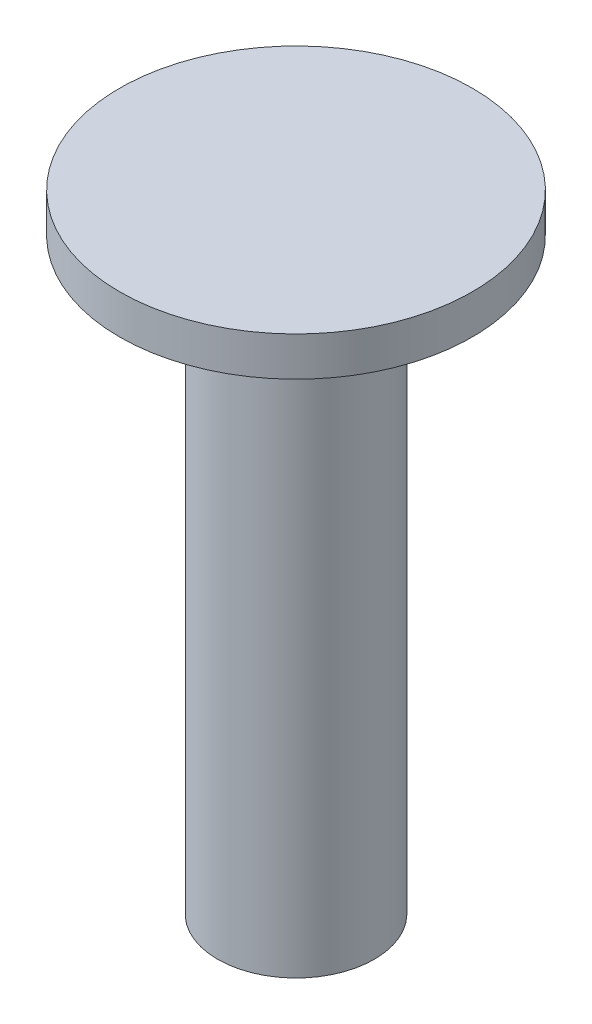
SolidWorks part; units mm, degrees
ref_plane "Front Plane" through (0, 0, 0) normal (0, 0, 1) x (1, 0, 0)
ref_plane "Top Plane" through (0, 0, 0) normal (0, 1, 0) x (1, 0, 0)
ref_plane "Right Plane" through (0, 0, 0) normal (1, 0, 0) x (0, 0, -1)
sketch "Sketch1" plane through (0, 0, 0) normal (0, 1, 0) x (1, 0, 0)
  circle A0 centre (0, 0) radius 4
  dimension "D1" = 8
extrude "Boss-Extrude1" add sketch "Sketch1" along normal blind 30
sketch "Sketch2" plane through (0, 30, 0) normal (0, 1, 0) x (1, 0, 0)
  circle A0 centre (0, 0) radius 9
  dimension "D1" = 18
extrude "Boss-Extrude2" add sketch "Sketch2" along normal blind 2
